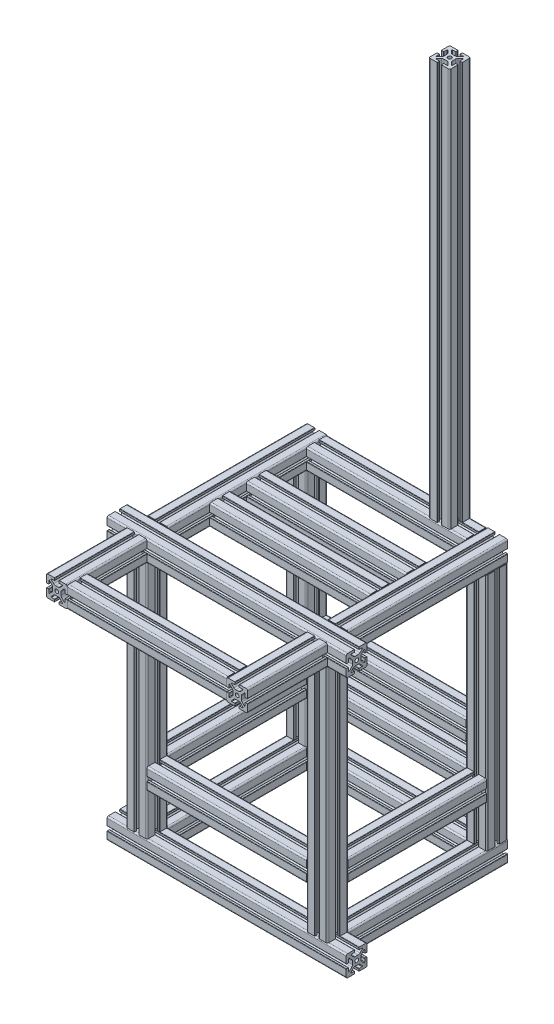
SolidWorks part; units mm, degrees
ref_plane "Front Plane" through (0, 0, 0) normal (0, 0, 1) x (1, 0, 0)
ref_plane "Top Plane" through (0, 0, 0) normal (0, 1, 0) x (1, 0, 0)
ref_plane "Right Plane" through (0, 0, 0) normal (1, 0, 0) x (0, 0, -1)
sketch3d "3DSketch2"
  line L0 (228.6, 0, 152.4) -> (-228.6, 0, 152.4)
  line L5 (172.4, 0, -152.4) -> (172.4, 0, 152.4) construction
  line L6 (172.4, 0, -152.4) -> (-172.4, 0, -152.4) construction
  line L15 (-172.4, 0, -152.4) -> (-172.4, 0, 152.4) construction
  line L16 (172.4, 0, 152.4) -> (-172.4, 0, 152.4) construction
  line L21 (172.4, 0, -152.4) -> (-172.4, 0, 152.4) construction
  line L22 (-172.4, 0, -152.4) -> (172.4, 0, 152.4) construction
  line L23 (172.4, 0, 132.4) -> (172.4, 0, -172.4)
  line L24 (-172.4, 0, 132.4) -> (-172.4, 0, -172.4)
  line L29 (-152.4, 0, -152.4) -> (152.4, 0, -152.4)
  line L30 (172.4, 0, -152.4) -> (172.4, 20, -152.4) construction
  line L31 (-172.4, 0, -152.4) -> (-172.4, 20, -152.4) construction
  line L32 (-172.4, 0, 152.4) -> (-172.4, 20, 152.4) construction
  line L34 (172.4, 0, 152.4) -> (172.4, 20, 152.4) construction
  line L36 (172.4, 20, -152.4) -> (172.4, 477.2, -152.4)
  line L37 (-172.4, 20, -152.4) -> (-172.4, 477.2, -152.4)
  line L38 (172.4, 20, 152.4) -> (172.4, 477.2, 152.4)
  line L39 (-172.4, 20, 152.4) -> (-172.4, 477.2, 152.4)
  line L40 (-172.4, 497.2, 152.4) -> (-172.4, 477.2, 152.4) construction
  line L41 (172.4, 497.2, 152.4) -> (172.4, 497.2, -152.4) construction
  line L42 (172.4, 497.2, 152.4) -> (-172.4, 497.2, 152.4) construction
  line L43 (-172.4, 497.2, 152.4) -> (-172.4, 497.2, -152.4) construction
  line L44 (172.4, 497.2, -152.4) -> (-172.4, 497.2, -152.4) construction
  line L45 (172.4, 497.2, 152.4) -> (172.4, 477.2, 152.4) construction
  line L46 (172.4, 497.2, -152.4) -> (172.4, 477.2, -152.4) construction
  line L47 (-172.4, 497.2, -152.4) -> (-172.4, 477.2, -152.4) construction
  line L48 (172.4, 497.2, 132.4) -> (172.4, 497.2, -172.4)
  line L49 (-172.4, 497.2, 132.4) -> (-172.4, 497.2, -172.4)
  line L50 (-152.4, 497.2, -152.4) -> (152.4, 497.2, -152.4)
  line L51 (-228.6, 497.2, 152.4) -> (228.6, 497.2, 152.4)
  line L52 (152.4, 120, -152.4) -> (-152.4, 120, -152.4)
  line L53 (172.4, 120, 152.4) -> (172.4, 120, -152.4) construction
  line L54 (172.4, 120, 152.4) -> (-172.4, 120, 152.4) construction
  line L55 (-172.4, 120, 152.4) -> (-172.4, 120, -152.4) construction
  line L56 (172.4, 120, -152.4) -> (-172.4, 120, -152.4) construction
  line L57 (152.4, 120, 152.4) -> (-152.4, 120, 152.4)
  line L58 (-172.4, 120, 132.4) -> (-172.4, 120, -132.4)
  line L59 (172.4, 120, 132.4) -> (172.4, 120, -132.4)
  line L60 (172.4, 120, 0) -> (-172.4, 120, 0) construction
  line L61 (-152.4, 120, 0) -> (152.4, 120, 0)
  line L62 (-152.4, 0, 0) -> (152.4, 0, 0)
  line L63 (-152.4, 0, 0) -> (-172.4, 0, 0) construction
  line L64 (101.6, 497.2, -152.4) -> (101.6, 517.2, -152.4) construction
  line L65 (101.6, 517.2, -152.4) -> (101.6, 1279.2, -152.4)
  line L66 (-172.4, 497.2, -37.6) -> (172.4, 497.2, -37.6) construction
  line L67 (-172.4, 497.2, 32.4) -> (172.4, 497.2, 32.4) construction
  line L68 (-152.4, 497.2, -37.6) -> (152.4, 497.2, -37.6)
  line L69 (-152.4, 497.2, 32.4) -> (152.4, 497.2, 32.4)
  line L70 (0, 497.2, -37.6) -> (0, 497.2, 32.4) construction
  line L71 (-172.4, 497.2, 152.4) -> (-172.4, 497.2, 172.4) construction
  line L72 (-172.4, 497.2, 172.4) -> (-172.4, 497.2, 324.8)
  line L73 (172.4, 497.2, 304.8) -> (-172.4, 497.2, 304.8) construction
  line L74 (-172.4, 497.2, 172.4) -> (-172.4, 497.2, 324.8) construction
  line L75 (-172.4, 497.2, 172.4) -> (172.4, 497.2, 172.4) construction
  line L76 (172.4, 497.2, 172.4) -> (172.4, 497.2, 324.8) construction
  line L78 (172.4, 497.2, 172.4) -> (172.4, 497.2, 324.8)
  line L79 (152.4, 497.2, 304.8) -> (-152.4, 497.2, 304.8)
  line L80 (172.4, 200, 132.4) -> (172.4, 200, -132.4)
  line L81 (172.4, 200, 152.4) -> (172.4, 200, -152.4) construction
  line L82 (172.4, 200, 152.4) -> (-172.4, 200, 152.4) construction
  line L83 (-172.4, 200, 152.4) -> (-172.4, 200, -152.4) construction
  line L84 (172.4, 200, -152.4) -> (-172.4, 200, -152.4) construction
  line L85 (152.4, 200, -152.4) -> (-152.4, 200, -152.4)
  line L86 (-172.4, 200, -132.4) -> (-172.4, 200, 132.4)
  line L87 (-152.4, 200, 152.4) -> (152.4, 200, 152.4)
  line L88 (-172.4, 200, 0) -> (172.4, 200, 0) construction
  line L89 (-152.4, 200, 0) -> (152.4, 200, 0)
  point P0 (0, 0, 0)
  point P9 (0, 0, 152.4)
  point P12 (0, 0, -152.4)
  point P71 (0, 497.2, -37.6)
  dimension "D6" = 20
  dimension "D1" = 457.2
  dimension "D5" = 304.8
  dimension "D2" = 20
  dimension "D3" = 304.8
  dimension "D4" = 20
  dimension "D7" = 20
  dimension "D8" = 457.2
  dimension "D9" = 20
  dimension "D10" = 100
  dimension "D11" = 20
  dimension "D12" = 20
  dimension "D13" = 264.8
  dimension "D14" = 304.8
  dimension "D15" = 20
  dimension "D16" = 20
  dimension "D17" = 762
  dimension "D18" = 50.8
  dimension "D19" = 70
  dimension "D21" = 20
  dimension "D22" = 304.8
  dimension "D23" = 20
  dimension "D24" = 152.4
  dimension "D25" = 20
  dimension "D26" = 80
  dimension "D20" = 120
other "4040 profiles 5537T711(1)"
ref_plane "Plane2" through (228.6, 0, 152.4) normal (-1, 0, 0) x (0, 0, 1)
sketch "Sketch41" plane through (228.6, 0, 152.4) normal (-1, 0, 0) x (0, 0, 1)
  line L0 (4.8, -20) -> (17.2, -20)
  line L1 (4, -20) -> (20, -20) construction
  line L2 (4, -20) -> (4, -15.3907) construction
  line L3 (4, -15.3907) -> (12.1314, -15.3907) construction
  line L4 (4, -16.1907) -> (4, -19.2)
  line L5 (4.8, -15.3907) -> (10.2, -15.3907)
  line L6 (-2.7525, -8) -> (2.7525, -8)
  line L7 (12.1314, -15.3907) -> (4.7407, -8) construction
  line L8 (6.1466, -9.4059) -> (10.7657, -14.025)
  line L9 (20, -20) -> (20, -4) construction
  line L10 (15.3907, -12.1314) -> (8, -4.7407) construction
  line L11 (15.3907, -4) -> (15.3907, -12.1314) construction
  line L12 (15.3907, -10.2) -> (15.3907, -4.8)
  line L13 (20, -4) -> (15.3907, -4) construction
  line L14 (16.1907, -4) -> (19.2, -4)
  line L15 (20, -4.8) -> (20, -17.2)
  line L16 (14.025, -10.7657) -> (9.4059, -6.1466)
  line L17 (8, 2.7525) -> (8, -2.7525)
  line L18 (-20, 0) -> (20, 0) construction
  line L19 (0, -8) -> (0, -3.5) construction
  line L20 (-6.1466, 9.4059) -> (-10.7657, 14.025)
  line L21 (8, 0) -> (3.5, 0) construction
  line L22 (0, 0) -> (0, 7.483) construction
  line L23 (0, 0) -> (-11.7338, 0) construction
  line L24 (-6.1466, -9.4059) -> (-10.7657, -14.025)
  line L25 (-4.8, -15.3907) -> (-10.2, -15.3907)
  line L26 (-4, -16.1907) -> (-4, -19.2)
  line L27 (-4.8, -20) -> (-17.2, -20)
  line L28 (-20, -4.8) -> (-20, -17.2)
  line L29 (-16.1907, -4) -> (-19.2, -4)
  line L30 (-15.3907, -10.2) -> (-15.3907, -4.8)
  line L31 (-14.025, -10.7657) -> (-9.4059, -6.1466)
  line L32 (-8, 2.7525) -> (-8, -2.7525)
  line L33 (-8, 0) -> (-3.5, 0) construction
  line L34 (-4.8, 15.3907) -> (-10.2, 15.3907)
  line L35 (-4, 16.1907) -> (-4, 19.2)
  line L36 (-4.8, 20) -> (-17.2, 20)
  line L37 (-20, 4.8) -> (-20, 17.2)
  line L38 (-16.1907, 4) -> (-19.2, 4)
  line L39 (-15.3907, 10.2) -> (-15.3907, 4.8)
  line L40 (-14.025, 10.7657) -> (-9.4059, 6.1466)
  line L41 (14.025, 10.7657) -> (9.4059, 6.1466)
  line L42 (15.3907, 10.2) -> (15.3907, 4.8)
  line L43 (16.1907, 4) -> (19.2, 4)
  line L44 (20, 4.8) -> (20, 17.2)
  line L45 (4.8, 20) -> (17.2, 20)
  line L46 (4, 16.1907) -> (4, 19.2)
  line L47 (4.8, 15.3907) -> (10.2, 15.3907)
  line L48 (6.1466, 9.4059) -> (10.7657, 14.025)
  line L49 (-2.7525, 8) -> (2.7525, 8)
  line L50 (-17.2, 20) -> (-20, 20) construction
  line L51 (-20, 17.2) -> (-20, 20) construction
  line L52 (17.2, 20) -> (20, 20) construction
  line L53 (20, 17.2) -> (20, 20) construction
  line L54 (-20, -17.2) -> (-20, -20) construction
  line L55 (-17.2, -20) -> (-20, -20) construction
  line L56 (20, -17.2) -> (20, -20) construction
  line L57 (17.2, -20) -> (20, -20) construction
  line L58 (20, 4.8) -> (20, -4.8) construction
  line L59 (8, 0) -> (20, 0) construction
  line L60 (-20, 4.8) -> (-20, -4.8) construction
  line L61 (-11.7338, 0) -> (-20, 0) construction
  arc A0 (4, -19.2) -> (4.8, -20) centre (4.8, -19.2) ccw
  arc A1 (10.2, -15.3907) -> (10.7657, -14.025) centre (10.2, -14.5907) ccw construction
  arc A2 (4, -16.1907) -> (4.8, -15.3907) centre (4.8, -16.1907) cw
  arc A3 (10.2, -15.3907) -> (10.7657, -14.025) centre (10.2, -14.5907) ccw
  arc A4 (2.7525, -8) -> (6.1466, -9.4059) centre (2.7525, -12.8) cw
  arc A5 (17.2, -20) -> (20, -17.2) centre (17.2, -17.2) ccw
  arc A6 (14.025, -10.7657) -> (15.3907, -10.2) centre (14.5907, -10.2) ccw
  arc A7 (15.3907, -4.8) -> (16.1907, -4) centre (16.1907, -4.8) cw
  arc A8 (19.2, -4) -> (20, -4.8) centre (19.2, -4.8) cw
  arc A9 (9.4059, -6.1466) -> (8, -2.7525) centre (12.8, -2.7525) cw
  circle A10 centre (0, 0) radius 3.5 construction
  circle A11 centre (0, 0) radius 3.5
  arc A12 (-2.7525, -8) -> (-6.1466, -9.4059) centre (-2.7525, -12.8) ccw
  arc A13 (-10.2, -15.3907) -> (-10.7657, -14.025) centre (-10.2, -14.5907) cw
  arc A14 (-4, -16.1907) -> (-4.8, -15.3907) centre (-4.8, -16.1907) ccw
  arc A15 (-4, -19.2) -> (-4.8, -20) centre (-4.8, -19.2) cw
  arc A16 (-17.2, -20) -> (-20, -17.2) centre (-17.2, -17.2) cw
  arc A17 (-19.2, -4) -> (-20, -4.8) centre (-19.2, -4.8) ccw
  arc A18 (-15.3907, -4.8) -> (-16.1907, -4) centre (-16.1907, -4.8) ccw
  arc A19 (-14.025, -10.7657) -> (-15.3907, -10.2) centre (-14.5907, -10.2) cw
  arc A20 (-9.4059, -6.1466) -> (-8, -2.7525) centre (-12.8, -2.7525) ccw
  arc A21 (-2.7525, 8) -> (-6.1466, 9.4059) centre (-2.7525, 12.8) cw
  arc A22 (-10.2, 15.3907) -> (-10.7657, 14.025) centre (-10.2, 14.5907) ccw
  arc A23 (-4, 16.1907) -> (-4.8, 15.3907) centre (-4.8, 16.1907) cw
  arc A24 (-4, 19.2) -> (-4.8, 20) centre (-4.8, 19.2) ccw
  arc A25 (-17.2, 20) -> (-20, 17.2) centre (-17.2, 17.2) ccw
  arc A26 (-19.2, 4) -> (-20, 4.8) centre (-19.2, 4.8) cw
  arc A27 (-15.3907, 4.8) -> (-16.1907, 4) centre (-16.1907, 4.8) cw
  arc A28 (-14.025, 10.7657) -> (-15.3907, 10.2) centre (-14.5907, 10.2) ccw
  arc A29 (-9.4059, 6.1466) -> (-8, 2.7525) centre (-12.8, 2.7525) cw
  arc A30 (9.4059, 6.1466) -> (8, 2.7525) centre (12.8, 2.7525) ccw
  arc A31 (14.025, 10.7657) -> (15.3907, 10.2) centre (14.5907, 10.2) cw
  arc A32 (15.3907, 4.8) -> (16.1907, 4) centre (16.1907, 4.8) ccw
  arc A33 (19.2, 4) -> (20, 4.8) centre (19.2, 4.8) ccw
  arc A34 (17.2, 20) -> (20, 17.2) centre (17.2, 17.2) cw
  arc A35 (4, 19.2) -> (4.8, 20) centre (4.8, 19.2) cw
  arc A36 (4, 16.1907) -> (4.8, 15.3907) centre (4.8, 16.1907) ccw
  arc A37 (10.2, 15.3907) -> (10.7657, 14.025) centre (10.2, 14.5907) cw
  arc A38 (2.7525, 8) -> (6.1466, 9.4059) centre (2.7525, 12.8) ccw
  point P145 (-19.1799, 19.1799)
  point P146 (19.1799, 19.1799)
  point P147 (19.1799, -19.1799)
  point P148 (-19.1799, -19.1799)
  point P155 (0, 0)
  dimension "D1" = 2.8
  dimension "D2" = 4.8
equation "\"ExtrusionOffset\"= 20mm"
equation "\"D6@3DSketch2\"=\"ExtrusionOffset\""
equation "\"D4@3DSketch2\"=\"D2@3DSketch2\""
equation "\"D7@3DSketch2\"=\"ExtrusionOffset\""
equation "\"D11@3DSketch2\"=\"ExtrusionOffset\""
equation "\"D12@3DSketch2\"=\"ExtrusionOffset\""
equation "\"D15@3DSketch2\"=\"ExtrusionOffset\""
equation "\"D16@3DSketch2\"=\"ExtrusionOffset\""
equation "\"D21@3DSketch2\"=\"ExtrusionOffset\""
equation "\"D23@3DSketch2\"=\"ExtrusionOffset\""
equation "\"D25@3DSketch2\"=\"ExtrusionOffset\""
